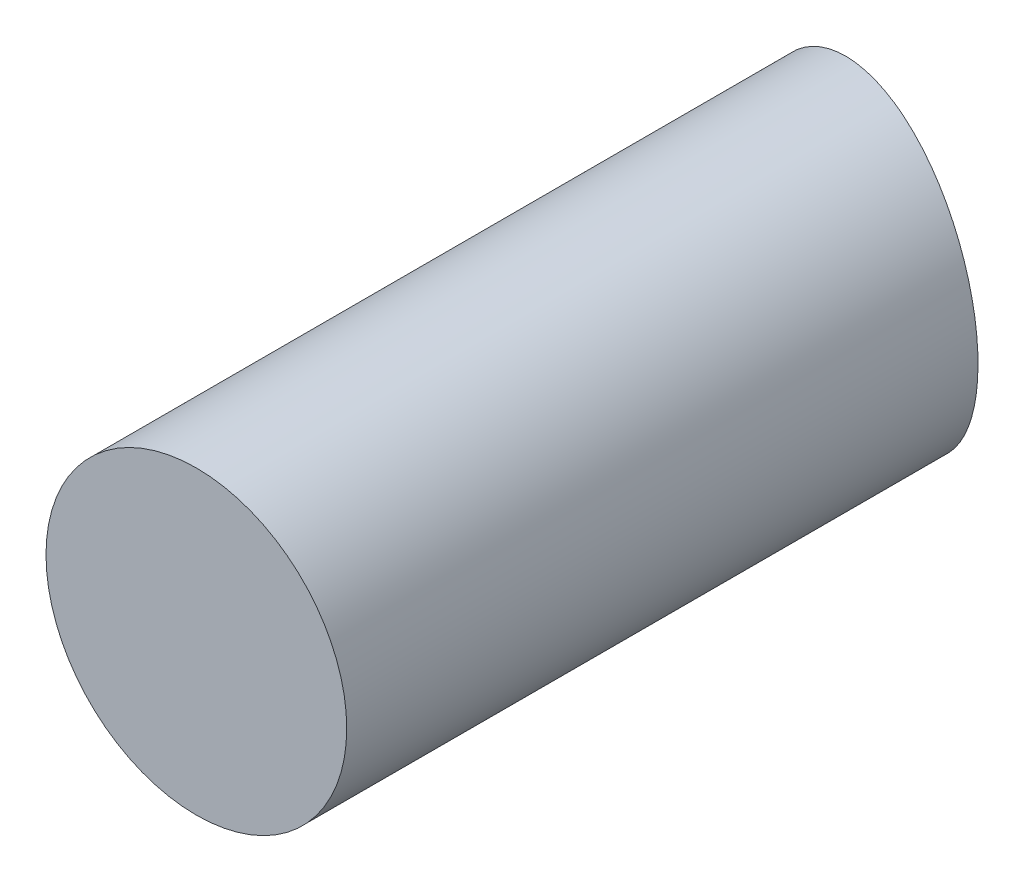
SolidWorks part; units mm, degrees
ref_plane "Front Plane" through (0, 0, 0) normal (0, 0, 1) x (1, 0, 0)
ref_plane "Top Plane" through (0, 0, 0) normal (0, 1, 0) x (1, 0, 0)
ref_plane "Right Plane" through (0, 0, 0) normal (1, 0, 0) x (0, 0, -1)
sketch "Sketch1" plane through (0, 0, 0) normal (0, 0, 1) x (1, 0, 0)
  line L0 (0, -4.7625) -> (0, 4.7625) construction
  circle A0 centre (0, 0) radius 4.7625
  dimension "D1" = 9.525
extrude "Boss-Extrude1" add sketch "Sketch1" along normal blind 25.4
ref_plane "Plane4" through (0, 0, 0) normal (-0.9659, 0, -0.2588) x (0, 1, 0)
sketch "Sketch2" plane through (0, 0, 0) normal (-0.9659, 0, -0.2588) x (0, 1, 0)
  line L0 (4.7625, 0) -> (-4.7625, 0)
  line L1 (0, 0) -> (0, -8.6727) construction
  line L2 (4.7625, -2.9373) -> (4.7625, 0)
  line L3 (-4.7625, 0) -> (-4.7625, -2.9373)
  ellipse E0 centre (0, 0) end of major axis (-4.7625, 0) minor radius 1.2326 construction
  ellipse E1 centre (0, 0) end of major axis (-4.7625, 0) minor radius 1.2326
  ellipse E3 centre (0, -2.9373) end of major axis (9.3628, -2.9373) minor radius 1.0513
extrude "Cut-Extrude1" cut sketch "Sketch2" against normal through all both and the other way through all contours E1 L1 E3 L2 | L1 E1 L3 E3 | L1 L0 E1 | L0 L1 E1 | L0 E1
